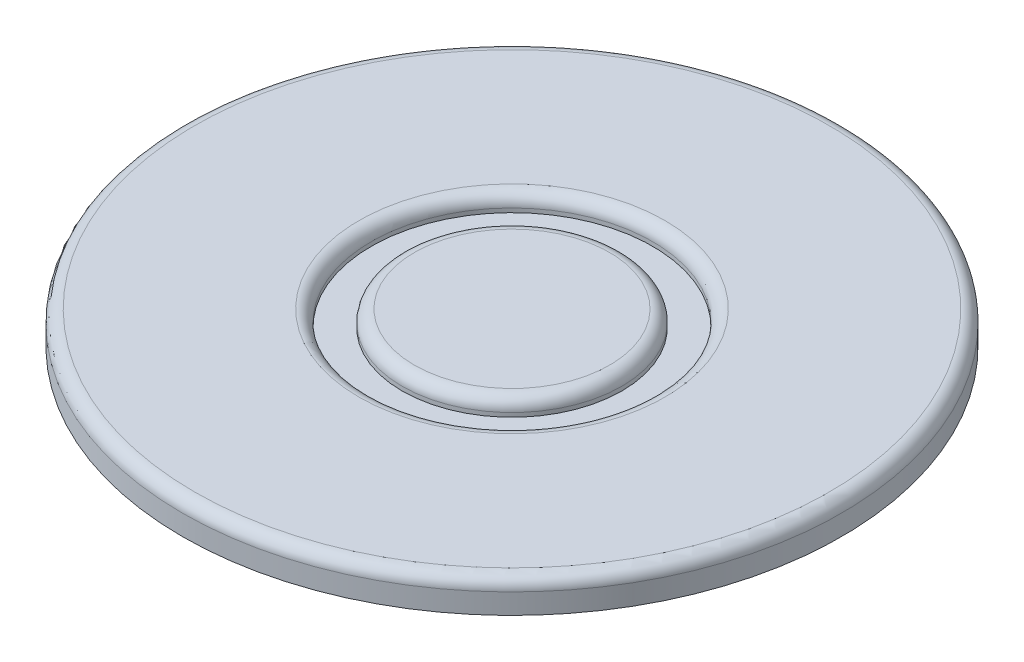
SolidWorks part; units mm, degrees
ref_plane "Alzado" through (0, 0, 0) normal (0, 0, 1) x (1, 0, 0)
ref_plane "Planta" through (0, 0, 0) normal (0, 1, 0) x (1, 0, 0)
ref_plane "Vista lateral" through (0, 0, 0) normal (1, 0, 0) x (0, 0, -1)
sketch "Croquis1" plane through (0, 0, 0) normal (0, 1, 0) x (1, 0, 0)
  circle A0 centre (0, 0) radius 40.5
  circle A1 centre (0, 0) radius 40.5
  circle A2 centre (0, 0) radius 17.3
  circle A3 centre (0, 0) radius 13.5
  circle A4 centre (0, 0) radius 45
  dimension "D1" = 4.5
  dimension "D2" = 81
  dimension "D3" = 34.6
  dimension "D4" = 27
  dimension "D5" = 90
extrude "Saliente-Extruir1" add sketch "Croquis1" along normal blind 2 contours A4 A0 | A1 A2 | A3
sketch "Croquis2" plane through (0, 0, 0) normal (0, -1, 0) x (1, 0, 0)
  circle A0 centre (0, 0) radius 45
  circle A1 centre (0, 0) radius 45 construction
  dimension "D1" = 0
extrude "Saliente-Extruir2" add sketch "Croquis2" along normal blind 2
sketch "Croquis3" plane through (0, 2, 0) normal (0, 1, 0) x (1, 0, 0)
  circle A0 centre (0, 0) radius 40.5
  circle A1 centre (0, 0) radius 56.4846
extrude "Cortar-Extruir1" cut sketch "Croquis3" against normal blind 10
fillet "Redondeo2" radius 1.5 3 edges at (0, 2, 17.3) (0, 2, 13.5) (0, 2, 40.5)
